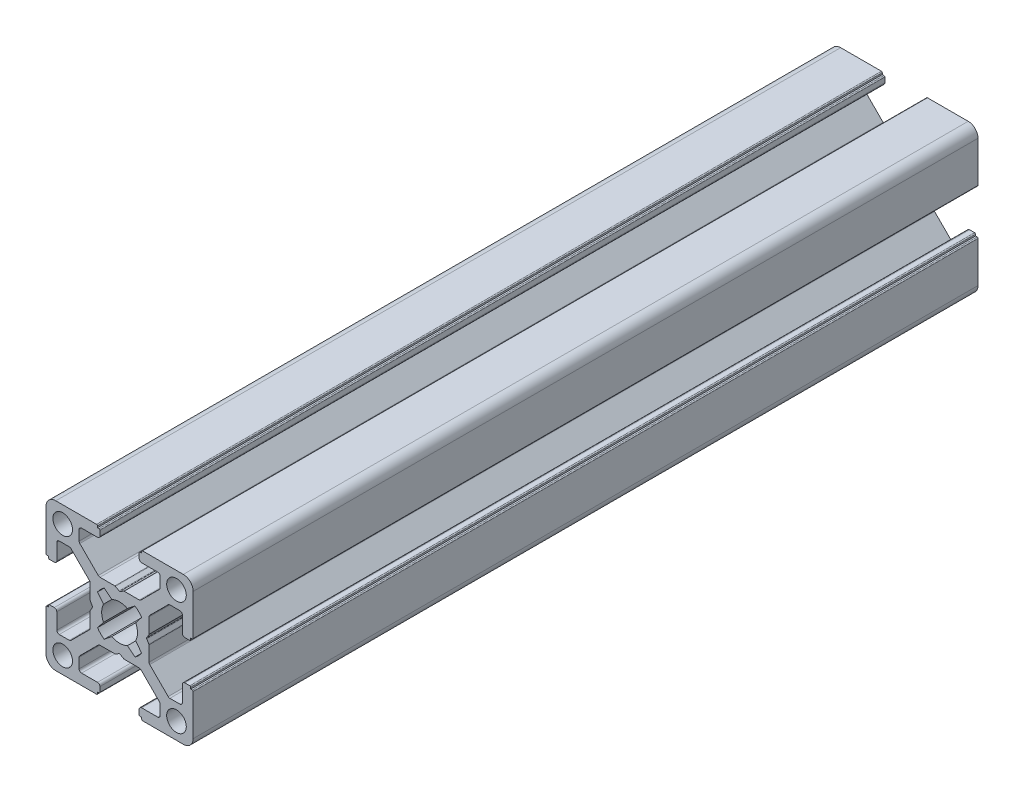
SolidWorks part; units mm, degrees
ref_plane "Alzado" through (0, 0, 0) normal (0, 0, 1) x (1, 0, 0)
ref_plane "Planta" through (0, 0, 0) normal (0, 1, 0) x (1, 0, 0)
ref_plane "Vista lateral" through (0, 0, 0) normal (1, 0, 0) x (0, 0, -1)
ref_plane "Plano1" through (0, 0, 1000) normal (0, 0, 1) x (1, 0, 0)
sketch "Croquis1" plane through (0, 0, 1000) normal (0, 0, 1) x (1, 0, 0)
  line L16 (-7.8359, -10.4816) -> (-6.3001, -11.7194)
  line L17 (-3.0999, -11.7194) -> (-1.5641, -10.4816)
  line L18 (-0.1947, -11.8453) -> (-1.4194, -13.3999)
  line L19 (-1.4194, -16.6001) -> (-0.1947, -18.1547)
  line L20 (-1.5641, -19.5184) -> (-3.0999, -18.2806)
  line L21 (-6.3001, -18.2806) -> (-7.8359, -19.5184)
  line L22 (-9.2053, -18.1547) -> (-7.9806, -16.6001)
  line L23 (-7.9806, -13.3999) -> (-9.2053, -11.8453)
  line L24 (9.8, -10.5) -> (10.1, -10.5)
  line L25 (10.3, -10.3) -> (10.3, -2)
  line L26 (8.3, 0) -> (0, 0)
  line L27 (-0.2, -0.2) -> (-0.2, -0.5)
  line L28 (-0.2, -0.5) -> (-0.5, -0.5)
  line L29 (-0.7, -0.7) -> (-0.7, -1.7)
  line L30 (-0.2, -2.2) -> (3.05, -2.2)
  line L31 (3.55, -2.7) -> (3.55, -4.7431)
  line L32 (3.4037, -5.0964) -> (-0.3491, -8.8534)
  line L33 (-0.7028, -9) -> (-3.7468, -9)
  line L34 (-3.8462, -9.0264) -> (-4.6006, -9.4583)
  line L35 (-4.7994, -9.4583) -> (-5.5538, -9.0264)
  line L36 (-5.6532, -9) -> (-8.6972, -9)
  line L37 (-9.0509, -8.8534) -> (-12.8037, -5.0964)
  line L38 (-12.95, -4.7431) -> (-12.95, -2.7)
  line L39 (-12.45, -2.2) -> (-9.2, -2.2)
  line L40 (-8.7, -1.7) -> (-8.7, -0.7)
  line L41 (-8.9, -0.5) -> (-9.2, -0.5)
  line L42 (-9.2, -0.5) -> (-9.2, -0.2)
  line L43 (-9.4, 0) -> (-17.7, 0)
  line L44 (-19.7, -2) -> (-19.7, -10.3)
  line L45 (-19.5, -10.5) -> (-19.2, -10.5)
  line L46 (-19.2, -10.5) -> (-19.2, -10.8)
  line L47 (-19, -11) -> (-18, -11)
  line L48 (-17.5, -10.5) -> (-17.5, -7.25)
  line L49 (-17, -6.75) -> (-14.9569, -6.75)
  line L50 (-14.6036, -6.8963) -> (-10.8466, -10.6491)
  line L51 (-10.7, -11.0028) -> (-10.7, -14.0468)
  line L52 (-10.6736, -14.1462) -> (-10.2417, -14.9006)
  line L53 (-10.2417, -15.0994) -> (-10.6736, -15.8538)
  line L54 (-10.7, -15.9532) -> (-10.7, -18.9972)
  line L55 (-10.8466, -19.3509) -> (-14.6036, -23.1037)
  line L56 (-14.9569, -23.25) -> (-17, -23.25)
  line L57 (-17.5, -22.75) -> (-17.5, -19.5)
  line L58 (-18, -19) -> (-19, -19)
  line L59 (-19.2, -19.2) -> (-19.2, -19.5)
  line L60 (-19.2, -19.5) -> (-19.5, -19.5)
  line L61 (-19.7, -19.7) -> (-19.7, -28)
  line L62 (-17.7, -30) -> (-9.4, -30)
  line L63 (-9.2, -29.8) -> (-9.2, -29.5)
  line L64 (-9.2, -29.5) -> (-8.9, -29.5)
  line L65 (-8.7, -29.3) -> (-8.7, -28.3)
  line L66 (-9.2, -27.8) -> (-12.45, -27.8)
  line L67 (-12.95, -27.3) -> (-12.95, -25.2569)
  line L68 (-12.8037, -24.9036) -> (-9.0509, -21.1466)
  line L69 (-8.6972, -21) -> (-5.6532, -21)
  line L70 (-5.5538, -20.9736) -> (-4.7994, -20.5417)
  line L71 (-4.6006, -20.5417) -> (-3.8462, -20.9736)
  line L72 (-3.7468, -21) -> (-0.7028, -21)
  line L73 (-0.3491, -21.1466) -> (3.4037, -24.9036)
  line L74 (3.55, -25.2569) -> (3.55, -27.3)
  line L75 (3.05, -27.8) -> (-0.2, -27.8)
  line L76 (-0.7, -28.3) -> (-0.7, -29.3)
  line L77 (-0.5, -29.5) -> (-0.2, -29.5)
  line L78 (-0.2, -29.5) -> (-0.2, -29.8)
  line L79 (0, -30) -> (8.3, -30)
  line L80 (10.3, -28) -> (10.3, -19.7)
  line L81 (10.1, -19.5) -> (9.8, -19.5)
  line L82 (9.8, -19.5) -> (9.8, -19.2)
  line L83 (9.6, -19) -> (8.6, -19)
  line L84 (8.1, -19.5) -> (8.1, -22.75)
  line L85 (7.6, -23.25) -> (5.5569, -23.25)
  line L86 (5.2036, -23.1037) -> (1.4466, -19.3509)
  line L87 (1.3, -18.9972) -> (1.3, -15.9532)
  line L88 (1.2736, -15.8538) -> (0.8417, -15.0994)
  line L89 (0.8417, -14.9006) -> (1.2736, -14.1462)
  line L90 (1.3, -14.0468) -> (1.3, -11.0028)
  line L91 (1.4466, -10.6491) -> (5.2036, -6.8963)
  line L92 (5.5569, -6.75) -> (7.6, -6.75)
  line L93 (8.1, -7.25) -> (8.1, -10.5)
  line L94 (8.6, -11) -> (9.6, -11)
  line L95 (9.8, -10.8) -> (9.8, -10.5)
  line L96 (8, -2.3) -> (5.8, -4.5) construction
  line L97 (-15.2, -2.3) -> (-17.4, -4.5) construction
  line L98 (-4.7, -15) -> (6.9, -15) construction
  arc A16 (-9.2053, -11.8453) -> (-7.8359, -10.4816) centre (-4.7, -15) cw
  arc A17 (-6.3001, -11.7194) -> (-3.0999, -11.7194) centre (-4.7, -15) cw
  arc A18 (-1.5641, -10.4816) -> (-0.1947, -11.8453) centre (-4.7, -15) cw
  arc A19 (-1.4194, -13.3999) -> (-1.4194, -16.6001) centre (-4.7, -15) cw
  arc A20 (-0.1947, -18.1547) -> (-1.5641, -19.5184) centre (-4.7, -15) cw
  arc A21 (-3.0999, -18.2806) -> (-6.3001, -18.2806) centre (-4.7, -15) cw
  arc A22 (-7.8359, -19.5184) -> (-9.2053, -18.1547) centre (-4.7, -15) cw
  arc A23 (-7.9806, -16.6001) -> (-7.9806, -13.3999) centre (-4.7, -15) cw
  arc A24 (10.1, -10.5) -> (10.3, -10.3) centre (10.1, -10.3) ccw
  arc A25 (10.3, -2) -> (8.3, 0) centre (8.3, -2) ccw
  arc A26 (0, 0) -> (-0.2, -0.2) centre (0, -0.2) ccw
  arc A27 (-0.5, -0.5) -> (-0.7, -0.7) centre (-0.5, -0.7) ccw
  arc A28 (-0.7, -1.7) -> (-0.2, -2.2) centre (-0.2, -1.7) ccw
  arc A29 (3.05, -2.2) -> (3.55, -2.7) centre (3.05, -2.7) cw
  arc A30 (3.55, -4.7431) -> (3.4037, -5.0964) centre (3.05, -4.7431) cw
  arc A31 (-0.3491, -8.8534) -> (-0.7028, -9) centre (-0.7028, -8.5) cw
  arc A32 (-3.7468, -9) -> (-3.8462, -9.0264) centre (-3.7468, -9.2) ccw
  arc A33 (-4.6006, -9.4583) -> (-4.7994, -9.4583) centre (-4.7, -9.2847) cw
  arc A34 (-5.5538, -9.0264) -> (-5.6532, -9) centre (-5.6532, -9.2) ccw
  arc A35 (-8.6972, -9) -> (-9.0509, -8.8534) centre (-8.6972, -8.5) cw
  arc A36 (-12.8037, -5.0964) -> (-12.95, -4.7431) centre (-12.45, -4.7431) cw
  arc A37 (-12.95, -2.7) -> (-12.45, -2.2) centre (-12.45, -2.7) cw
  arc A38 (-9.2, -2.2) -> (-8.7, -1.7) centre (-9.2, -1.7) ccw
  arc A39 (-8.7, -0.7) -> (-8.9, -0.5) centre (-8.9, -0.7) ccw
  arc A40 (-9.2, -0.2) -> (-9.4, 0) centre (-9.4, -0.2) ccw
  arc A41 (-17.7, 0) -> (-19.7, -2) centre (-17.7, -2) ccw
  arc A42 (-19.7, -10.3) -> (-19.5, -10.5) centre (-19.5, -10.3) ccw
  arc A43 (-19.2, -10.8) -> (-19, -11) centre (-19, -10.8) ccw
  arc A44 (-18, -11) -> (-17.5, -10.5) centre (-18, -10.5) ccw
  arc A45 (-17.5, -7.25) -> (-17, -6.75) centre (-17, -7.25) cw
  arc A46 (-14.9569, -6.75) -> (-14.6036, -6.8963) centre (-14.9569, -7.25) cw
  arc A47 (-10.8466, -10.6491) -> (-10.7, -11.0028) centre (-11.2, -11.0028) cw
  arc A48 (-10.7, -14.0468) -> (-10.6736, -14.1462) centre (-10.5, -14.0468) ccw
  arc A49 (-10.2417, -14.9006) -> (-10.2417, -15.0994) centre (-10.4153, -15) cw
  arc A50 (-10.6736, -15.8538) -> (-10.7, -15.9532) centre (-10.5, -15.9532) ccw
  arc A51 (-10.7, -18.9972) -> (-10.8466, -19.3509) centre (-11.2, -18.9972) cw
  arc A52 (-14.6036, -23.1037) -> (-14.9569, -23.25) centre (-14.9569, -22.75) cw
  arc A53 (-17, -23.25) -> (-17.5, -22.75) centre (-17, -22.75) cw
  arc A54 (-17.5, -19.5) -> (-18, -19) centre (-18, -19.5) ccw
  arc A55 (-19, -19) -> (-19.2, -19.2) centre (-19, -19.2) ccw
  arc A56 (-19.5, -19.5) -> (-19.7, -19.7) centre (-19.5, -19.7) ccw
  arc A57 (-19.7, -28) -> (-17.7, -30) centre (-17.7, -28) ccw
  arc A58 (-9.4, -30) -> (-9.2, -29.8) centre (-9.4, -29.8) ccw
  arc A59 (-8.9, -29.5) -> (-8.7, -29.3) centre (-8.9, -29.3) ccw
  arc A60 (-8.7, -28.3) -> (-9.2, -27.8) centre (-9.2, -28.3) ccw
  arc A61 (-12.45, -27.8) -> (-12.95, -27.3) centre (-12.45, -27.3) cw
  arc A62 (-12.95, -25.2569) -> (-12.8037, -24.9036) centre (-12.45, -25.2569) cw
  arc A63 (-9.0509, -21.1466) -> (-8.6972, -21) centre (-8.6972, -21.5) cw
  arc A64 (-5.6532, -21) -> (-5.5538, -20.9736) centre (-5.6532, -20.8) ccw
  arc A65 (-4.7994, -20.5417) -> (-4.6006, -20.5417) centre (-4.7, -20.7153) cw
  arc A66 (-3.8462, -20.9736) -> (-3.7468, -21) centre (-3.7468, -20.8) ccw
  arc A67 (-0.7028, -21) -> (-0.3491, -21.1466) centre (-0.7028, -21.5) cw
  arc A68 (3.4037, -24.9036) -> (3.55, -25.2569) centre (3.05, -25.2569) cw
  arc A69 (3.55, -27.3) -> (3.05, -27.8) centre (3.05, -27.3) cw
  arc A70 (-0.2, -27.8) -> (-0.7, -28.3) centre (-0.2, -28.3) ccw
  arc A71 (-0.7, -29.3) -> (-0.5, -29.5) centre (-0.5, -29.3) ccw
  arc A72 (-0.2, -29.8) -> (0, -30) centre (0, -29.8) ccw
  arc A73 (8.3, -30) -> (10.3, -28) centre (8.3, -28) ccw
  arc A74 (10.3, -19.7) -> (10.1, -19.5) centre (10.1, -19.7) ccw
  arc A75 (9.8, -19.2) -> (9.6, -19) centre (9.6, -19.2) ccw
  arc A76 (8.6, -19) -> (8.1, -19.5) centre (8.6, -19.5) ccw
  arc A77 (8.1, -22.75) -> (7.6, -23.25) centre (7.6, -22.75) cw
  arc A78 (5.5569, -23.25) -> (5.2036, -23.1037) centre (5.5569, -22.75) cw
  arc A79 (1.4466, -19.3509) -> (1.3, -18.9972) centre (1.8, -18.9972) cw
  arc A80 (1.3, -15.9532) -> (1.2736, -15.8538) centre (1.1, -15.9532) ccw
  arc A81 (0.8417, -15.0994) -> (0.8417, -14.9006) centre (1.0153, -15) cw
  arc A82 (1.2736, -14.1462) -> (1.3, -14.0468) centre (1.1, -14.0468) ccw
  arc A83 (1.3, -11.0028) -> (1.4466, -10.6491) centre (1.8, -11.0028) cw
  arc A84 (5.2036, -6.8963) -> (5.5569, -6.75) centre (5.5569, -7.25) cw
  arc A85 (7.6, -6.75) -> (8.1, -7.25) centre (7.6, -7.25) cw
  arc A86 (8.1, -10.5) -> (8.6, -11) centre (8.6, -10.5) ccw
  arc A87 (9.6, -11) -> (9.8, -10.8) centre (9.6, -10.8) ccw
  circle A88 centre (-16.3, -3.4) radius 2
  circle A89 centre (6.9, -3.4) radius 2
  circle A90 centre (-16.3, -26.6) radius 2
  circle A91 centre (6.9, -26.6) radius 2
  dimension "D3" = 4
  dimension "D1" = 30
  dimension "D2" = 30
  dimension "D4" = 23.2
  dimension "D5" = 23.2
extrude "Saliente-Extruir1" add sketch "Croquis1" against normal blind 160
